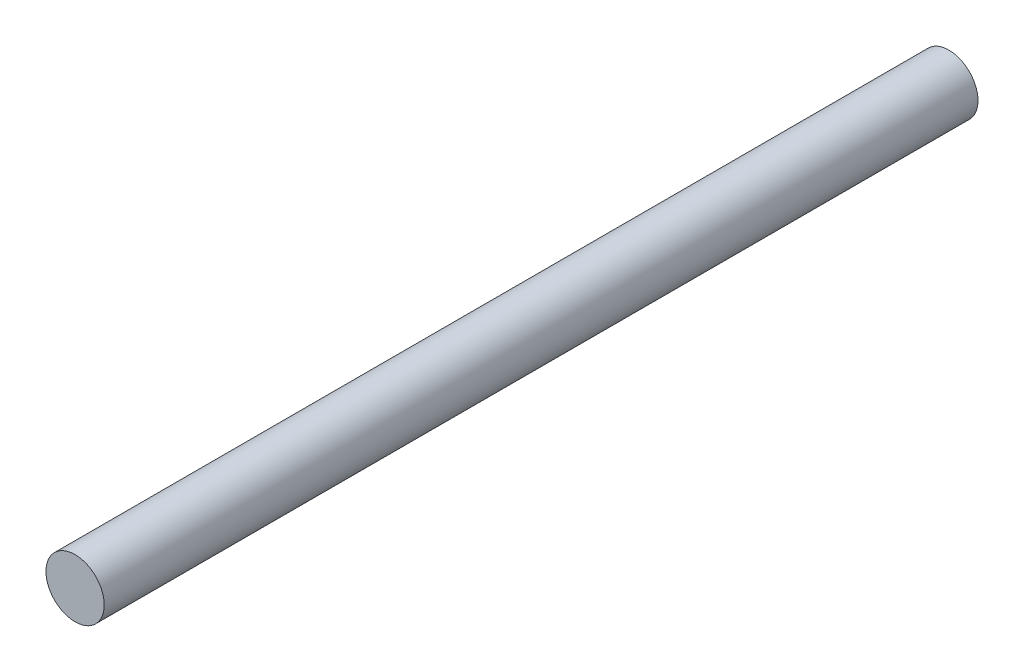
SolidWorks part; units mm, degrees
ref_plane "Front Plane" through (0, 0, 0) normal (0, 0, 1) x (1, 0, 0)
ref_plane "Top Plane" through (0, 0, 0) normal (0, 1, 0) x (1, 0, 0)
ref_plane "Right Plane" through (0, 0, 0) normal (1, 0, 0) x (0, 0, -1)
sketch "Sketch1" plane through (0, 0, 0) normal (0, 0, 1) x (1, 0, 0)
  circle A0 centre (0, 0) radius 2.5
  dimension "D1" = 5
extrude "Boss-Extrude1" add sketch "Sketch1" along normal blind 75
